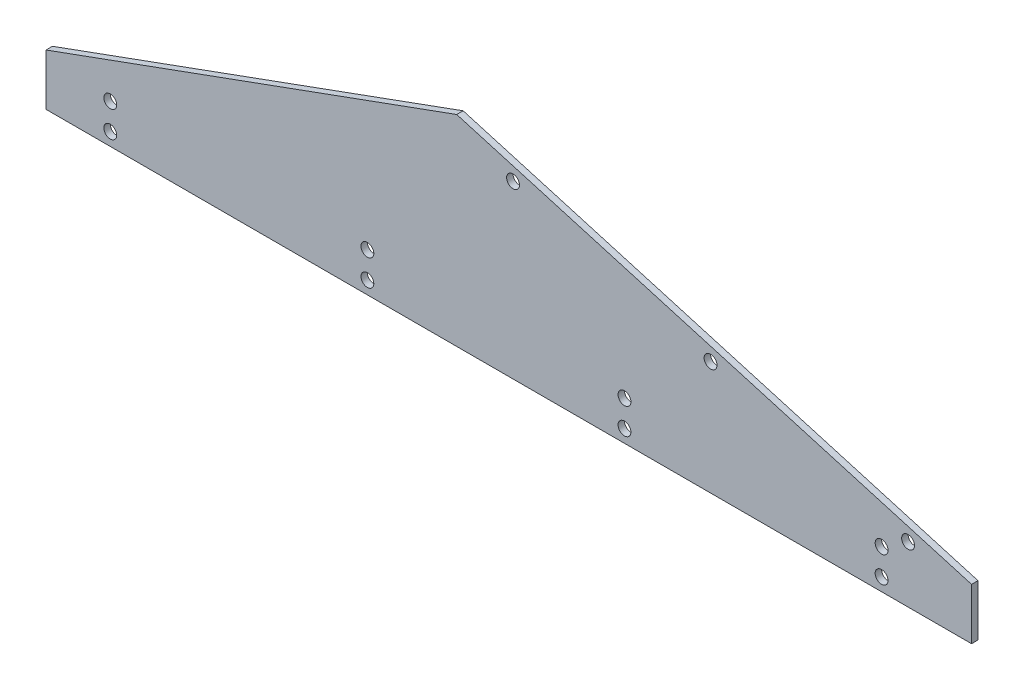
SolidWorks part; units mm, degrees
ref_plane "Front Plane" through (0, 0, 0) normal (0, 0, 1) x (1, 0, 0)
ref_plane "Top Plane" through (0, 0, 0) normal (0, 1, 0) x (1, 0, 0)
ref_plane "Right Plane" through (0, 0, 0) normal (1, 0, 0) x (0, 0, -1)
sketch "Sketch1" plane through (0, 0, 0) normal (0, 0, 1) x (1, 0, 0)
  line L0 (0, 0) -> (457.2, 0)
  line L1 (457.2, 0) -> (457.2, 25.4)
  line L2 (457.2, 25.4) -> (202.8796, 99.2421)
  line L3 (202.8796, 99.2421) -> (0, 25.4)
  line L4 (0, 25.4) -> (0, 0)
  line L5 (202.8796, 99.2421) -> (457.2, 25.4) construction
  line L6 (202.8796, 99.2421) -> (201.109, 93.144) construction
  line L7 (457.2, 25.4) -> (455.4294, 19.3018) construction
  line L8 (201.109, 93.144) -> (455.4294, 19.3018) construction
  line L10 (0, 19.3018) -> (457.2, 19.3018) construction
  line L11 (0, 19.3018) -> (0, 6.35) construction
  line L12 (0, 6.35) -> (457.2, 6.35) construction
  line L13 (457.2, 19.3018) -> (457.2, 6.35) construction
  circle A0 centre (230.6988, 84.5526) radius 3.175
  circle A1 centre (328.2692, 56.2229) radius 3.175
  circle A2 centre (425.8397, 27.8933) radius 3.175
  circle A3 centre (31.75, 19.3018) radius 3.175
  circle A4 centre (31.75, 6.35) radius 3.175
  circle A5 centre (158.75, 19.3018) radius 3.175
  circle A6 centre (285.75, 19.3018) radius 3.175
  circle A7 centre (412.75, 19.3018) radius 3.175
  circle A8 centre (158.75, 6.35) radius 3.175
  circle A9 centre (285.75, 6.35) radius 3.175
  circle A10 centre (412.75, 6.35) radius 3.175
  dimension "D6" = 6.35
  dimension "D8" = 6.35
  dimension "D9" = 6.35
  dimension "D12" = 6.35
  dimension "D13" = 6.35
  dimension "D1" = 457.2
  dimension "D2" = 110
  dimension "D3" = 25.4
  dimension "D4" = 215.9
  dimension "D5" = 6.35
  dimension "D7" = 101.6
  dimension "D10" = 101.6
  dimension "D11" = 6.35
  dimension "D14" = 31.75
  dimension "D17" = 127
  dimension "D15" = 4
  dimension "D16" = 4
extrude "Boss-Extrude1" add sketch "Sketch1" along normal blind 3.175
